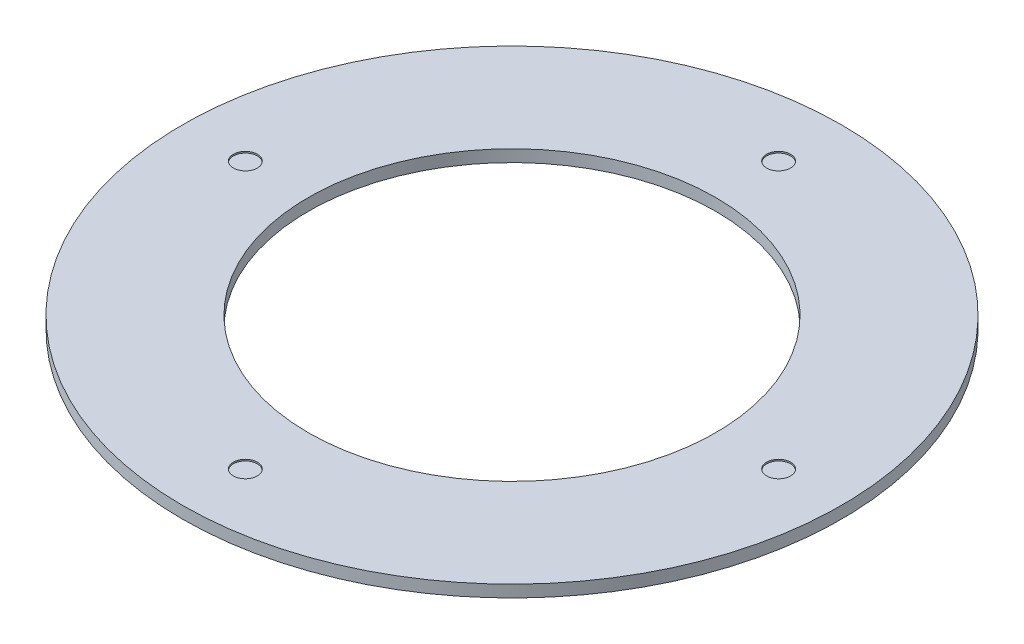
SolidWorks part; units mm, degrees
ref_plane "Front Plane" through (0, 0, 0) normal (0, 0, 1) x (1, 0, 0)
ref_plane "Top Plane" through (0, 0, 0) normal (0, 1, 0) x (1, 0, 0)
ref_plane "Right Plane" through (0, 0, 0) normal (1, 0, 0) x (0, 0, -1)
sketch "Sketch1" plane through (0, 0, 0) normal (0, 1, 0) x (1, 0, 0)
  circle A0 centre (0, 0) radius 55
  dimension "D1" = 110
extrude "Boss-Extrude1" add sketch "Sketch1" along normal blind 2
sketch "Sketch2" plane through (0, 2, 0) normal (0, 1, 0) x (1, 0, 0)
  line L0 (0, 55) -> (0, -55) construction
  line L1 (0, -55) -> (-55, 0) construction
  line L2 (-55, 0) -> (55, 0) construction
  circle A0 centre (0, 0) radius 55 construction
  circle A1 centre (0, 0) radius 44.5
  circle A2 centre (0, 44.5) radius 2
  circle A3 centre (44.5, 0) radius 2
  circle A4 centre (0, -44.5) radius 2
  circle A5 centre (-44.5, 0) radius 2
  dimension "D1" = 10.5
  dimension "D2" = 4
  dimension "D3" = 4
  dimension "D4" = 4
  dimension "D5" = 4
extrude "Cut-Extrude1" cut sketch "Sketch2" against normal blind 0.25 contours A1 A4 | A1 A4 | A3 | A2 | A5
sketch "Sketch3" plane through (0, 2, 0) normal (0, 1, 0) x (1, 0, 0)
  line L0 (0, 0) -> (-55, 0) construction
  circle A0 centre (0, 0) radius 34
  circle A2 centre (0, 0) radius 55 construction
  circle A4 centre (-44.5, 0) radius 2 construction
  point P3 (-34, 0)
  dimension "D1" = 10.5
  dimension "D2" = 10.5
extrude "Cut-Extrude2" cut sketch "Sketch3" against normal blind 10 contours A0
